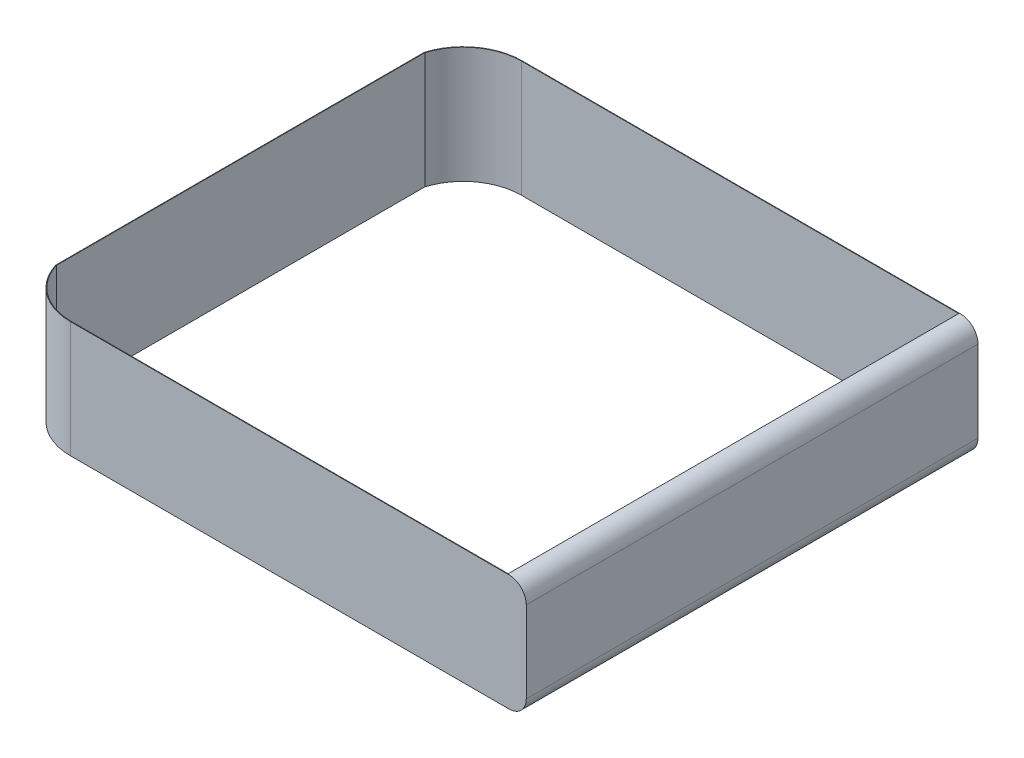
SolidWorks part; units mm, degrees
ref_plane "Front Plane" through (0, 0, 0) normal (0, 0, 1) x (1, 0, 0)
ref_plane "Top Plane" through (0, 0, 0) normal (0, 1, 0) x (1, 0, 0)
ref_plane "Right Plane" through (0, 0, 0) normal (1, 0, 0) x (0, 0, -1)
sketch "Sketch1" plane through (0, 0, 0) normal (0, 0, 1) x (1, 0, 0)
  line L0 (-1262.2956, 1976) -> (8389.7044, 1976)
  line L1 (8704.507, 293.1973) -> (8389.7044, 293.1973)
  line L2 (8389.7044, 0) -> (8389.7044, 293.1973)
  line L3 (-1262.2956, 0) -> (8389.7044, 0)
  line L4 (8704.507, 1682.8027) -> (8704.507, 293.1973)
  line L5 (8704.507, 988) -> (6681.3395, 988)
  line L6 (8389.7044, 1976) -> (8389.7044, 1682.8027)
  line L7 (8704.507, 1682.8027) -> (8389.7044, 1682.8027)
  arc A0 (8389.7044, 0) -> (8704.507, 293.1973) centre (8389.7044, 315.5987) ccw
  arc A1 (8389.7044, 1976) -> (8704.507, 1682.8027) centre (8389.7044, 1660.4013) cw
  point P6 (9892.6888, 988)
sketch "Sketch3" plane through (0, 0, 0) normal (0, 1, 0) x (1, 0, 0)
  line L0 (955.2644, -1000) -> (8389.7044, -1000) construction
  line L1 (8389.7044, -8680) -> (955.2644, -8680)
  line L2 (8389.7044, -9680) -> (8389.7044, 0) construction
  line L3 (955.2644, -8680) -> (8389.7044, -8680) construction
  line L5 (0, -1706.2625) -> (0, -7973.7375)
  line L8 (8389.7044, -1000) -> (955.2644, -1000)
  arc A0 (955.2644, -1000) -> (0, -1706.2625) centre (955.2644, -1999.1588) ccw
  arc A1 (955.2644, -8680) -> (0, -7973.7375) centre (955.2644, -7680.8412) cw
  point P11 (0, -1706.2625)
extrude "Extrude-Thin1" add sketch "Sketch3" along normal blind 1976 thin contours L8 A0 L5 A1 L1
sketch "Sketch6" plane through (0, 0, 1000) normal (0, 0, -1) x (-1, 0, 0)
  line L0 (-8706.6678, 1679.8672) -> (-8706.6678, 296.1328)
  line L2 (-8389.7044, 0) -> (-8389.7044, 1976)
  arc A0 (-8706.6678, 1679.8672) -> (-8389.7044, 1976) centre (-8409.8505, 1679.8672) cw
  arc A1 (-8706.6678, 296.1328) -> (-8389.7044, 0) centre (-8409.8505, 296.1328) ccw
extrude "Boss-Extrude1" add sketch "Sketch6" against normal blind 7680
sketch "Sketch4" plane through (0, 0, 9680) normal (0, 0, 1) x (1, 0, 0)
  line L0 (8389.7044, 0) -> (8389.7044, 1866)
  line L1 (8389.7044, 1007.3054) -> (8594.507, 1007.3054)
  line L2 (8594.507, 1678.476) -> (8594.507, 297.524) construction
  arc A0 (8594.507, 1678.476) -> (8389.7044, 1866) centre (8389.7044, 1660.4013) ccw construction
